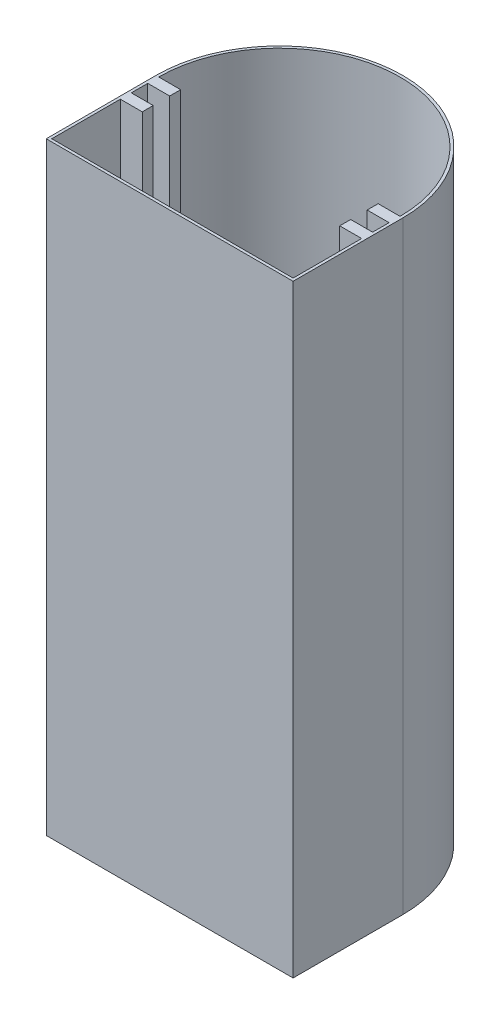
SolidWorks part; units mm, degrees
ref_plane "Front Plane" through (0, 0, 0) normal (0, 0, 1) x (1, 0, 0)
ref_plane "Top Plane" through (0, 0, 0) normal (0, 1, 0) x (1, 0, 0)
ref_plane "Right Plane" through (0, 0, 0) normal (1, 0, 0) x (0, 0, -1)
sketch "Sketch1" plane through (0, 0, 0) normal (0, 1, 0) x (1, 0, 0)
  line L0 (-43.8831, -1.7077) -> (1.1169, -1.7077)
  line L2 (-43.8831, -1.7077) -> (-43.8831, 18.2923)
  line L4 (1.1169, -1.7077) -> (1.1169, 18.2923)
  arc A0 (1.1169, 18.2923) -> (-43.8831, 18.2923) centre (-21.3831, 18.2923) ccw
  dimension "D3" = 22.5
  dimension "D1" = 45
  dimension "D2" = 20
extrude "Boss-Extrude1" add sketch "Sketch1" along normal blind 110 contours L2 A0 L4 L0
sketch "Sketch2" plane through (0, 110, 0) normal (0, 1, 0) x (1, 0, 0)
  line L5 (-43.3831, 16.2923) -> (-43.3831, 13.2923)
  line L6 (-43.3831, -1.2077) -> (0.6169, -1.2077)
  line L8 (-43.3831, 18.2923) -> (-39.3831, 18.2923)
  line L9 (-39.3831, 18.2923) -> (-39.3831, 16.2923)
  line L10 (-39.3831, 16.2923) -> (-43.3831, 16.2923)
  line L12 (-43.3831, 13.2923) -> (-39.3831, 13.2923)
  line L13 (-39.3831, 13.2923) -> (-39.3831, 11.2923)
  line L14 (-39.3831, 11.2923) -> (-43.3831, 11.2923)
  line L15 (0.6169, 11.2923) -> (0.6169, -1.2077)
  line L16 (-43.3831, 11.2923) -> (-43.3831, -1.2077)
  line L17 (-3.3831, 11.2923) -> (0.6169, 11.2923)
  line L18 (-3.3831, 13.2923) -> (-3.3831, 11.2923)
  line L19 (0.6169, 13.2923) -> (-3.3831, 13.2923)
  line L20 (-3.3831, 16.2923) -> (0.6169, 16.2923)
  line L21 (-3.3831, 18.2923) -> (-3.3831, 16.2923)
  line L22 (0.6169, 18.2923) -> (-3.3831, 18.2923)
  line L23 (-43.8831, -1.7077) -> (1.1169, -1.7077) construction
  line L24 (-43.8831, -1.7077) -> (-43.8831, 18.2923) construction
  line L25 (0.6169, 16.2923) -> (0.6169, 13.2923)
  arc A4 (0.6169, 18.2923) -> (-43.3831, 18.2923) centre (-21.3831, 18.2923) ccw
  point P7 (0, 0)
  point P8 (0, 0)
  point P25 (-21.3831, -1.2077)
  dimension "D1" = 4
  dimension "D2" = 2
  dimension "D3" = 3
  dimension "D4" = 2
  dimension "D5" = 4
  dimension "D6" = 0.5
  dimension "D7" = 0.5
  dimension "D8" = 4
  dimension "D9" = 3
  dimension "D10" = 2
  dimension "D11" = 2
extrude "Cut-Extrude1" cut sketch "Sketch2" against normal blind 109.5
sketch "Sketch3" plane through (-43.8831, 0, 0) normal (-1, 0, 0) x (0, 0, 1)
  line L0 (1.7077, 110) -> (1.7077, 0) construction
  line L1 (1.7077, 110) -> (-18.2923, 110) construction
  circle A0 centre (-4.9589, 55) radius 2.875
  point P4 (0, 0)
  dimension "D1" = 5.75
  dimension "D2" = 6.6667
  dimension "D3" = 55
extrude "Cut-Extrude2" cut sketch "Sketch3" against normal blind 5
equation "\"Width\"= 45"
equation "\"Depth\"= 20"
equation "\"lenght\"= 110"
equation "\"thick\"= 0.5"
equation "\"D1@Sketch1\"=\"Width\""
equation "\"D3@Sketch1\"=\"Width\"/2"
equation "\"length\"= 110"
equation "\"D1@Boss-Extrude1\"=\"length\""
equation "\"holder lenght\"= 4"
equation "\"holder width\"= 2"
equation "\"holder gap\"= 3"
equation "\"D1@Sketch2\"=\"holder lenght\""
equation "\"D2@Sketch2\"=\"holder width\""
equation "\"D3@Sketch2\"=\"holder gap\""
equation "\"D4@Sketch2\"=\"holder width\""
equation "\"D5@Sketch2\"=\"holder lenght\""
equation "\"D6@Sketch2\"=\"thick\""
equation "\"D7@Sketch2\"=\"thick\""
equation "\"D1@Cut-Extrude1\"=\"length\"-\"thick\""
equation "\"fillet\"= 0.5"
equation "\"D2@Sketch1\"=\"Depth\""
equation "\"D8@Sketch2\"=\"holder lenght\""
equation "\"D9@Sketch2\"=\"holder gap\""
equation "\"D10@Sketch2\"=\"holder width\""
equation "\"D11@Sketch2\"=\"holder width\""
equation "\"hole\"=5.75"
equation "\"D1@Sketch3\"=\"hole\""
equation "\"D2@Sketch3\"=\"Depth\"/3"
equation "\"D3@Sketch3\"=\"lenght\"/2"
